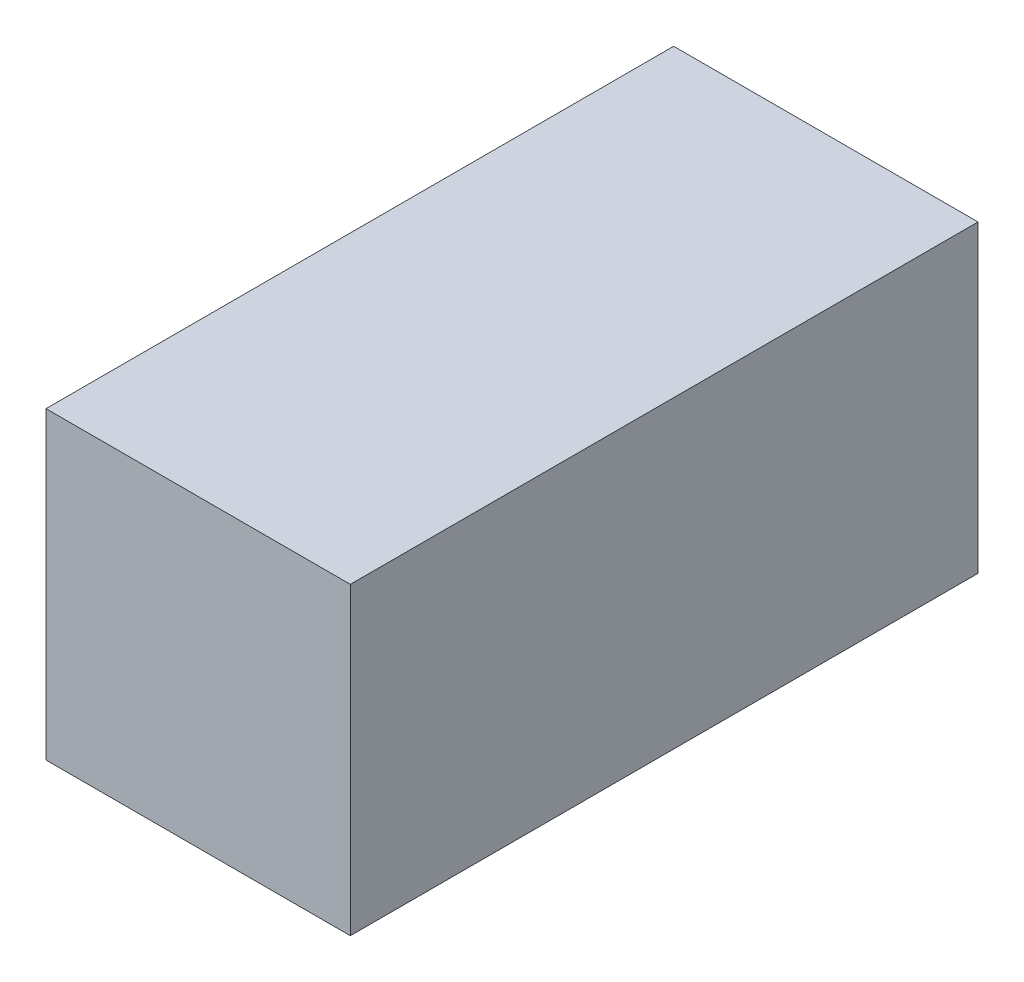
SolidWorks part; units mm, degrees
ref_plane "Plan de face" through (0, 0, 0) normal (0, 0, 1) x (1, 0, 0)
ref_plane "Plan de dessus" through (0, 0, 0) normal (0, 1, 0) x (1, 0, 0)
ref_plane "Plan de droite" through (0, 0, 0) normal (1, 0, 0) x (0, 0, -1)
sketch "Esquisse1" plane through (0, 0, 0) normal (0, 0, 1) x (1, 0, 0)
  line L1 (-30.9498, 23.5206) -> (49.0502, 23.5206)
  line L2 (-30.9498, 23.5206) -> (-30.9498, -56.4794)
  line L3 (-30.9498, -56.4794) -> (49.0502, -56.4794)
  line L4 (49.0502, 23.5206) -> (49.0502, -56.4794)
  dimension "D1" = 80
  dimension "D2" = 80
extrude "Boss.-Extru.1" add sketch "Esquisse1" along normal blind 165
